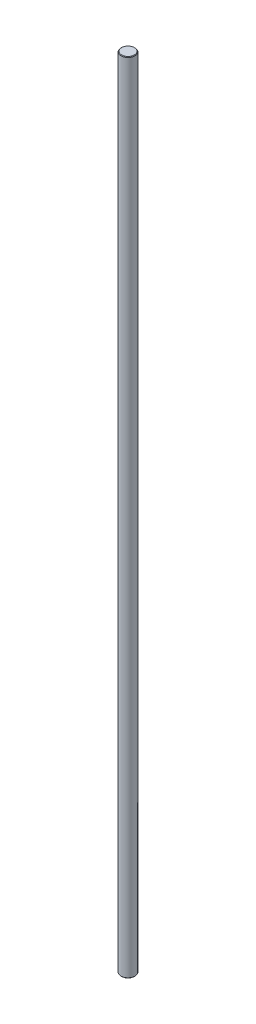
SolidWorks part; units mm, degrees
material "1023 Carbon Steel Sheet (SS)"
ref_plane "Front Plane" through (0, 0, 0) normal (0, 0, 1) x (1, 0, 0)
ref_plane "Top Plane" through (0, 0, 0) normal (0, 1, 0) x (1, 0, 0)
ref_plane "Right Plane" through (0, 0, 0) normal (1, 0, 0) x (0, 0, -1)
sketch "Sketch1" plane through (0, 0, 0) normal (0, 1, 0) x (1, 0, 0)
  circle A0 centre (0, 0) radius 2.5
  dimension "D1" = 5
extrude "Boss-Extrude1" add sketch "Sketch1" along normal blind 287
chamfer "Chamfer1" distance 0.2 angle 45 2 edges at (0, 0, 2.5) (0, 287, 2.5)
